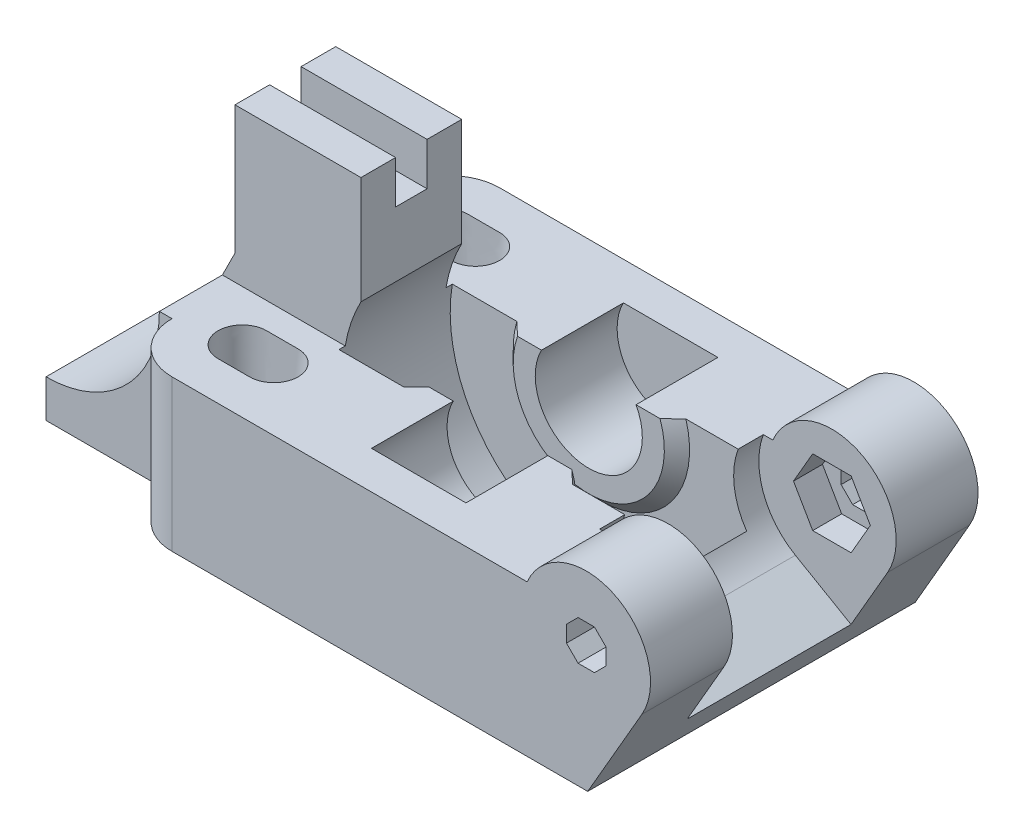
SolidWorks part; units mm, degrees
ref_plane "Front Plane" through (0, 0, 0) normal (0, 0, 1) x (1, 0, 0)
ref_plane "Top Plane" through (0, 0, 0) normal (0, 1, 0) x (1, 0, 0)
ref_plane "Right Plane" through (0, 0, 0) normal (1, 0, 0) x (0, 0, -1)
sketch "Sketch1" plane through (0, 0, 0) normal (0, 0, 1) x (1, 0, 0)
  line L0 (0, 0) -> (0, 12)
  line L1 (0, 12) -> (32.193, 12)
  line L2 (0, 0) -> (37, 0)
  line L3 (37, 0) -> (41.3013, 7.45)
  arc A0 (32.193, 12) -> (41.3013, 7.45) centre (36.8845, 10) cw
  point P5 (36.8845, 10)
  point P8 (20.5845, 10)
  dimension "D1" = 5.1
  dimension "D2" = 10
  dimension "D3" = 120
  dimension "D4" = 37
  dimension "D5" = 12
  dimension "D6" = 10
  dimension "D7" = 16.3
sketch "Sketch2" plane through (0, 0, 0) normal (0, 0, 1) x (1, 0, 0)
  line L0 (0, 12) -> (32.193, 12) construction
  line L1 (37, 0) -> (41.3013, 7.45) construction
  line L2 (0, 0) -> (37, 0) construction
  line L3 (0, 0) -> (0, 12) construction
  line L4 (0, 12) -> (32.193, 12)
  line L5 (37, 0) -> (41.3013, 7.45)
  line L6 (0, 0) -> (37, 0)
  line L7 (0, 0) -> (0, 12)
  arc A0 (41.3013, 7.45) -> (32.193, 12) centre (36.8845, 10) ccw construction
  arc A1 (41.3013, 7.45) -> (32.193, 12) centre (36.8845, 10) ccw
extrude "Boss-Extrude1" add sketch "Sketch2" along normal mid plane 26
sketch "Sketch12" plane through (0, 12, 0) normal (0, 1, 0) x (1, 0, 0)
  line L0 (0, 0) -> (32.193, 0) construction
  line L1 (0, -4) -> (10, -4)
  line L2 (0, -4) -> (0, 4)
  line L3 (0, 4) -> (10, 4)
  line L4 (10, -4) -> (10, 4)
  line L5 (0, -4) -> (10, 4) construction
  line L6 (0, 4) -> (10, -4) construction
  line L7 (0, -13) -> (0, 13) construction
  point P0 (5, 0)
  dimension "D1" = 8
  dimension "D2" = 10
extrude "Boss-Extrude2" add sketch "Sketch12" along normal blind 12.2
sketch "Sketch13" plane through (10, 0, 0) normal (1, 0, 0) x (0, 0, -1)
  line L0 (-4, 24.2) -> (4, 24.2) construction
  line L1 (-1.25, 24.2) -> (1.25, 24.2)
  line L2 (-1.25, 24.2) -> (-1.25, 20.8)
  line L3 (-1.25, 20.8) -> (1.25, 20.8)
  line L4 (1.25, 24.2) -> (1.25, 20.8)
  line L5 (-1.25, 24.2) -> (1.25, 20.8) construction
  line L6 (-1.25, 20.8) -> (1.25, 24.2) construction
  point P0 (0, 22.5)
  point P7 (0, 24.2)
  dimension "D1" = 3.4
  dimension "D2" = 2.5
extrude "Cut-Extrude8" cut sketch "Sketch13" against normal up to next
sketch "Sketch3" plane through (0, 0, 0) normal (0, 0, 1) x (1, 0, 0)
  circle A0 centre (20.5845, 10) radius 12
  dimension "D1" = 24
extrude "Cut-Extrude1" cut sketch "Sketch3" against normal mid plane 9
sketch "Sketch4" plane through (0, 0, -4.5) normal (0, 0, 1) x (1, 0, 0)
  circle A0 centre (20.5845, 10) radius 4.25
  dimension "D1" = 8.5
extrude "Cut-Extrude2" cut sketch "Sketch4" against normal blind 5.5
ref_plane "Plane1" through (20.5845, 0, 0) normal (1, 0, 0) x (0, 0, -1)
sketch "Sketch6" plane through (20.5845, 0, 0) normal (1, 0, 0) x (0, 0, -1)
  line L0 (4.5, 5.75) -> (3.5, 5.75)
  line L1 (3.5, 5.75) -> (3.5, 4)
  line L2 (3.5, 4) -> (4.5, 3)
  line L3 (4.5, 3) -> (4.5, 5.75)
  line L4 (0, 10) -> (7.3222, 10) construction
  dimension "D1" = 1
  dimension "D2" = 45
  dimension "D3" = 7
revolve "Revolve1" add sketch "Sketch6" angle 360 about L4
sketch "Sketch7" plane through (0, 0, -4.5) normal (0, 0, -1) x (-1, 0, 0)
  line L2 (-16.8345, 12) -> (-13.8763, 12)
  line L3 (-27.2927, 12) -> (-24.3345, 12)
  line L4 (-16.8345, 12) -> (-13.8763, 12)
  line L5 (-27.2927, 12) -> (-24.3345, 12)
  arc A2 (-13.8763, 12) -> (-27.2927, 12) centre (-20.5845, 10) ccw
  arc A3 (-16.8345, 12) -> (-24.3345, 12) centre (-20.5845, 10) ccw
  arc A4 (-13.8763, 12) -> (-27.2927, 12) centre (-20.5845, 10) ccw
  arc A5 (-16.8345, 12) -> (-24.3345, 12) centre (-20.5845, 10) ccw
  dimension "D1" = 0
extrude "Cut-Extrude3" cut sketch "Sketch7" against normal up to next (1 mm away)
sketch "Sketch8" plane through (0, 0, 0) normal (0, 0, 1) x (1, 0, 0)
  line L0 (33.9845, 4.9771) -> (38.4013, 2.4271)
  line L1 (37, 0) -> (41.3013, 7.45) construction
  line L3 (38.4013, 2.4271) -> (42.6824, 9.8422)
  arc A0 (33.9845, 4.9771) -> (42.6824, 9.8422) centre (36.8845, 10) cw
  dimension "D1" = 5.8
extrude "Cut-Extrude4" cut sketch "Sketch8" against normal blind 6.5
sketch "Sketch9" plane through (0, 0, -13) normal (0, 0, -1) x (-1, 0, 0)
  line L1 (-35.3139, 9.3494) -> (-35.3139, 10.6506)
  line L2 (-35.3139, 10.6506) -> (-36.234, 11.5706)
  line L3 (-36.234, 11.5706) -> (-37.5351, 11.5706)
  line L4 (-37.5351, 11.5706) -> (-38.4551, 10.6506)
  line L5 (-38.4551, 10.6506) -> (-38.4551, 9.3494)
  line L6 (-38.4551, 9.3494) -> (-37.5351, 8.4294)
  line L7 (-37.5351, 8.4294) -> (-36.234, 8.4294)
  line L8 (-36.234, 8.4294) -> (-35.3139, 9.3494)
  circle A0 centre (-36.8845, 10) radius 1.5706 construction
  dimension "D1" = 3.4
extrude "Cut-Extrude5" cut sketch "Sketch9" against normal up to next (6.5 mm away)
sketch "Sketch10" plane through (0, 0, -6.5) normal (0, 0, 1) x (1, 0, 0)
  line L1 (39.9345, 10) -> (38.4095, 12.6414)
  line L2 (38.4095, 12.6414) -> (35.3595, 12.6414)
  line L3 (35.3595, 12.6414) -> (33.8345, 10)
  line L4 (33.8345, 10) -> (35.3595, 7.3586)
  line L5 (35.3595, 7.3586) -> (38.4095, 7.3586)
  line L6 (38.4095, 7.3586) -> (39.9345, 10)
  circle A0 centre (36.8845, 10) radius 2.6414 construction
  dimension "D1" = 6.1
extrude "Cut-Extrude6" cut sketch "Sketch10" against normal blind 2.3
sketch "Sketch11" plane through (0, 0, 0) normal (0, 1, 0) x (1, 0, 0)
  line L0 (4.5845, 8) -> (5.5845, 8) construction
  line L1 (4.5845, 9.925) -> (5.5845, 9.925)
  line L2 (4.5845, 6.075) -> (5.5845, 6.075)
  line L3 (32.193, 13) -> (0, 13) construction
  line L4 (-5.0363, 0) -> (46.9928, 0) construction
  line L5 (0, 0) -> (37, 0) construction
  arc A0 (4.5845, 9.925) -> (4.5845, 6.075) centre (4.5845, 8) ccw
  arc A1 (5.5845, 6.075) -> (5.5845, 9.925) centre (5.5845, 8) ccw
  point P2 (5.0845, 8)
  point P7 (2.6595, 8)
  point P8 (7.5095, 8)
  dimension "D1" = 4.85
  dimension "D2" = 3.85
  dimension "D3" = 5
  dimension "D4" = 15.5
sketch "Sketch17" plane through (0, 12, 0) normal (0, 1, 0) x (1, 0, 0)
  line L0 (4.5845, 8) -> (7.0845, 8) construction
  line L1 (4.5845, 9.925) -> (7.0845, 9.925)
  line L2 (4.5845, 6.075) -> (7.0845, 6.075)
  line L3 (4.5845, 9.925) -> (5.5845, 9.925) construction
  arc A0 (4.5845, 9.925) -> (4.5845, 6.075) centre (4.5845, 8) ccw
  arc A1 (7.0845, 6.075) -> (7.0845, 9.925) centre (7.0845, 8) ccw
  point P3 (5.8345, 8)
  dimension "D1" = 1.5
loft "Cut-Loft3" cut profiles "Sketch11", "Sketch17"
fillet "Fillet1" radius 4 2 edges at (0, 6, -13) (0, 6, 13)
mirror "Mirror8" about plane through (0, 0, 0) normal (0, 0, 1) of "Cut-Loft3", "Cut-Extrude2", "Revolve1", "Cut-Extrude6", "Cut-Extrude5", "Cut-Extrude3", "Cut-Extrude4"
sketch "Sketch14" plane through (0, 0, 0) normal (0, 0, 1) x (1, 0, 0)
  line L0 (0, 0) -> (-10, 0)
  line L1 (-10, 0) -> (-10, 3)
  line L2 (0, 0) -> (0, 12) construction
  line L5 (-1, 12) -> (0, 12)
  line L6 (0, 12) -> (0, 0)
  line L7 (-1, 12) -> (-1, 0) construction
  line L8 (-10, 3) -> (0, 3) construction
  arc A0 (-10, 3) -> (-1, 12) centre (-10, 12) ccw
  dimension "D1" = 1
  dimension "D2" = 9
extrude "Boss-Extrude3" add sketch "Sketch14" along normal mid plane 18
sketch "Sketch15" plane through (0, 0, 4) normal (0, 0, 1) x (1, 0, 0)
  line L0 (0, 12) -> (0, 14)
  line L1 (0, 24.2) -> (0, 12) construction
  line L2 (0, 14) -> (-1, 12)
  line L3 (-1, 12) -> (0, 12)
  dimension "D1" = 2
extrude "Boss-Extrude4" add sketch "Sketch15" against normal up to surface (8 mm away)
